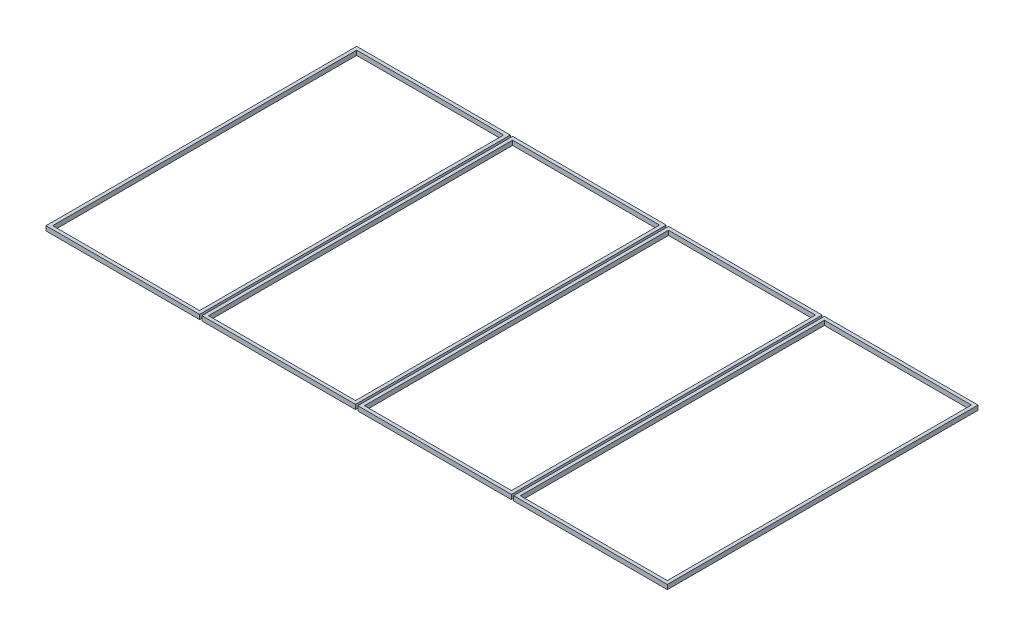
SolidWorks part; units mm, degrees
ref_plane "Front Plane" through (0, 0, 0) normal (0, 0, 1) x (1, 0, 0)
ref_plane "Top Plane" through (0, 0, 0) normal (0, 1, 0) x (1, 0, 0)
ref_plane "Right Plane" through (0, 0, 0) normal (1, 0, 0) x (0, 0, -1)
sketch "Sketch1" plane through (0, 0, 0) normal (0, 1, 0) x (1, 0, 0)
  line L0 (22, 1198) -> (581.25, 1198) construction
  line L2 (0, 0) -> (0, 1220)
  line L3 (0, 1220) -> (603.25, 1220)
  line L4 (2440, 0) -> (2440, 1220)
  line L5 (13, 1207) -> (590.25, 1207)
  line L9 (581.25, 1198) -> (581.25, 22) construction
  line L10 (13, 1207) -> (13, 13)
  line L11 (13, 13) -> (590.25, 13)
  line L12 (590.25, 1207) -> (590.25, 13)
  line L13 (625.25, 1207) -> (1202.5, 1207)
  line L14 (625.25, 1207) -> (625.25, 13)
  line L15 (625.25, 13) -> (1202.5, 13)
  line L16 (1202.5, 1207) -> (1202.5, 13)
  line L17 (0, 0) -> (13, 0)
  line L18 (13, 0) -> (590.25, 0)
  line L19 (590.25, 0) -> (603.25, 0)
  line L20 (625.25, 0) -> (1202.5, 0)
  line L21 (1237.5, 13) -> (1814.75, 13)
  line L22 (1237.5, 13) -> (1237.5, 1207)
  line L23 (1237.5, 1207) -> (1814.75, 1207)
  line L24 (1814.75, 13) -> (1814.75, 1207)
  line L25 (603.25, 0) -> (612.25, 0) construction
  line L26 (1237.5, 0) -> (1814.75, 0)
  line L27 (612.25, 0) -> (625.25, 0)
  line L28 (1849.75, 0) -> (2427, 0)
  line L29 (2427, 0) -> (2440, 0)
  line L30 (22, 22) -> (581.25, 22) construction
  line L31 (1849.75, 1207) -> (2427, 1207)
  line L32 (1849.75, 1207) -> (1849.75, 13)
  line L33 (1849.75, 13) -> (2427, 13)
  line L34 (2427, 1207) -> (2427, 13)
  line L35 (22, 1198) -> (22, 22) construction
  line L36 (634.25, 1198) -> (1193.5, 1198) construction
  line L37 (1193.5, 1198) -> (1193.5, 22) construction
  line L38 (634.25, 22) -> (1193.5, 22) construction
  line L39 (634.25, 1198) -> (634.25, 22) construction
  line L40 (1246.5, 1198) -> (1805.75, 1198) construction
  line L41 (1805.75, 22) -> (1805.75, 1198) construction
  line L42 (1246.5, 22) -> (1805.75, 22) construction
  line L43 (1246.5, 22) -> (1246.5, 1198) construction
  line L44 (1858.75, 1198) -> (1858.75, 22) construction
  line L45 (1858.75, 22) -> (2418, 22) construction
  line L46 (2418, 1198) -> (2418, 22) construction
  line L47 (1858.75, 1198) -> (2418, 1198) construction
  line L48 (1202.5, 0) -> (1215.5, 0)
  line L49 (1215.5, 0) -> (1224.5, 0) construction
  line L50 (1224.5, 0) -> (1237.5, 0)
  line L51 (1814.75, 0) -> (1827.75, 0)
  line L52 (1827.75, 0) -> (1836.75, 0) construction
  line L53 (1836.75, 0) -> (1849.75, 0)
  line L54 (603.25, 0) -> (603.25, 1220)
  line L55 (612.25, 0) -> (612.25, 1220)
  line L56 (1215.5, 0) -> (1215.5, 1220)
  line L57 (1224.5, 0) -> (1224.5, 1220)
  line L58 (1827.75, 0) -> (1827.75, 1220)
  line L59 (1836.75, 0) -> (1836.75, 1220)
  line L60 (612.25, 1220) -> (1215.5, 1220)
  line L61 (603.25, 1220) -> (612.25, 1220) construction
  line L62 (1224.5, 1220) -> (1827.75, 1220)
  line L63 (1215.5, 1220) -> (1224.5, 1220) construction
  line L64 (1836.75, 1220) -> (2440, 1220)
  line L65 (1827.75, 1220) -> (1836.75, 1220) construction
  dimension "D1" = 2440
  dimension "D2" = 1220
  dimension "D8" = 13
  dimension "D3" = 13
  dimension "D4" = 13
  dimension "D7" = 1176
  dimension "D10" = 559.25
  dimension "D11" = 612.25
  dimension "D9" = 13
  dimension "D12" = 9
  dimension "D5" = 9
  dimension "D6" = 9
extrude "Boss.-Extru.1" add sketch "Sketch1" along normal blind 18
equation "\"D12@Sketch1\"=\"tool_diameter\""
equation "\"tool_diameter\"=9"
equation "\"hole_clearance\"=0.5"
equation "\"material_thickness\"=18"
equation "\"clearance\"=0.5"
equation "\"outer_slot\"=0.5"
equation "\"fillet\"=7"
equation "\"D1@Boss.-Extru.1\"=\"material_thickness\""
equation "\"D5@Sketch1\"=\"tool_diameter\""
equation "\"D6@Sketch1\"=\"D5@Sketch1\""
